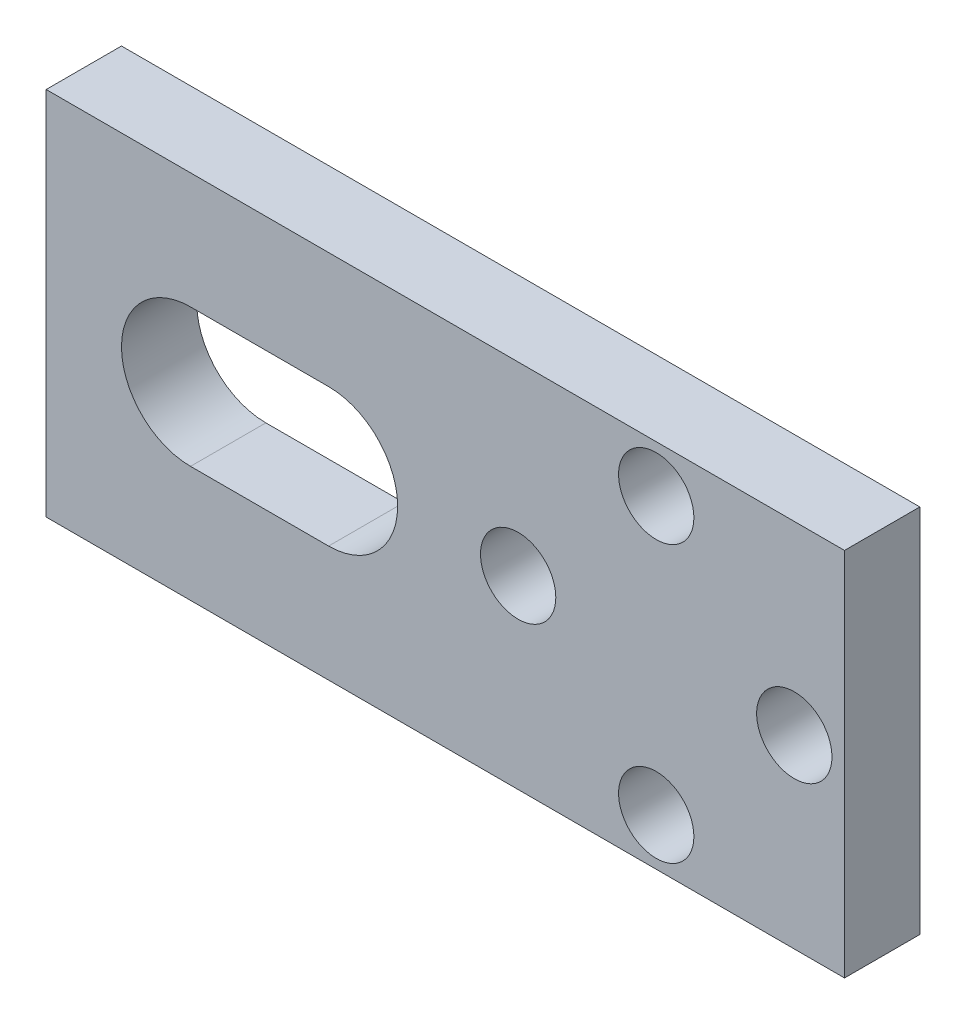
SolidWorks part; units mm, degrees
ref_plane "Front Plane" through (0, 0, 0) normal (0, 0, 1) x (1, 0, 0)
ref_plane "Top Plane" through (0, 0, 0) normal (0, 1, 0) x (1, 0, 0)
ref_plane "Right Plane" through (0, 0, 0) normal (1, 0, 0) x (0, 0, -1)
sketch "Sketch1" plane through (0, 0, 0) normal (0, 0, 1) x (1, 0, 0)
  line L0 (0, 7.375) -> (31.8, 7.375) construction
  line L1 (0, 0) -> (31.8, 0)
  line L2 (0, 0) -> (0, 14.75)
  line L3 (0, 14.75) -> (31.8, 14.75)
  line L4 (31.8, 0) -> (31.8, 14.75)
  line L5 (5.75, 7.375) -> (11.25, 7.375) construction
  line L6 (5.75, 10.125) -> (11.25, 10.125)
  line L7 (5.75, 4.625) -> (11.25, 4.625)
  line L8 (24.3, 14.75) -> (24.3, 0) construction
  arc A0 (5.75, 10.125) -> (5.75, 4.625) centre (5.75, 7.375) ccw
  arc A1 (11.25, 4.625) -> (11.25, 10.125) centre (11.25, 7.375) ccw
  circle A2 centre (29.8, 7.375) radius 1.5
  circle A3 centre (18.8, 7.375) radius 1.5
  circle A4 centre (24.3, 12.875) radius 1.5
  circle A5 centre (24.3, 1.875) radius 1.5
  point P9 (8.5, 7.375)
  dimension "D6" = 3
  dimension "D1" = 31.8
  dimension "D2" = 14.75
  dimension "D3" = 5.5
  dimension "D4" = 5.5
  dimension "D5" = 5.75
  dimension "D7" = 5.5
  dimension "D8" = 5.5
  dimension "D9" = 2
  dimension "D10" = 11
  dimension "D11" = 5.5
extrude "Boss-Extrude1" add sketch "Sketch1" along normal blind 3
ref_plane "Plane1" through (0, 7.375, 0) normal (0, 1, 0) x (1, 0, 0)
